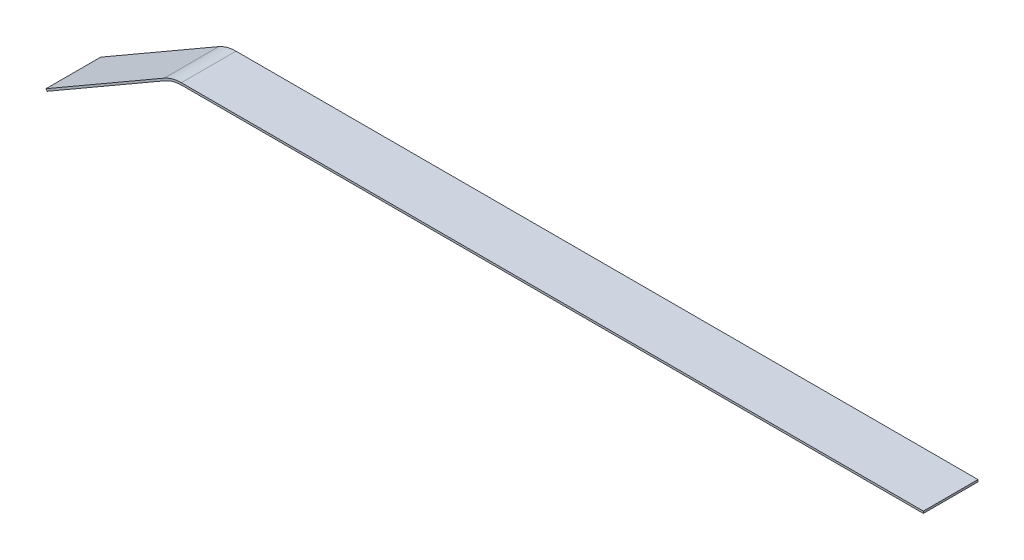
SolidWorks part; units mm, degrees
ref_plane "Front Plane" through (0, 0, 0) normal (0, 0, 1) x (1, 0, 0)
ref_plane "Top Plane" through (0, 0, 0) normal (0, 1, 0) x (1, 0, 0)
ref_plane "Right Plane" through (0, 0, 0) normal (1, 0, 0) x (0, 0, -1)
sketch "Sketch1" plane through (0, 0, 0) normal (0, 0, 1) x (1, 0, 0)
  line L0 (-1284.8076, -106.6987) -> (-1111.6025, -6.6987)
  line L1 (-1086.6025, 0) -> (0, 0)
  line L2 (0, 0) -> (0, -3)
  line L3 (0, -3) -> (-1085.7987, -3)
  line L4 (-1110.7987, -9.6987) -> (-1283.3076, -109.2968)
  line L5 (-1283.3076, -109.2968) -> (-1284.8076, -106.6987)
  arc A0 (-1110.7987, -9.6987) -> (-1085.7987, -3) centre (-1085.7987, -53) cw
  arc A1 (-1111.6025, -6.6987) -> (-1086.6025, 0) centre (-1086.6025, -50) cw
  point P11 (-1100, 0)
  dimension "D4" = 50
  dimension "D5" = 50
  dimension "D1" = 1100
  dimension "D2" = 3
  dimension "D3" = 3
  dimension "D6" = 150
  dimension "D7" = 200
extrude "Boss-Extrude1" add sketch "Sketch1" along normal blind 80
